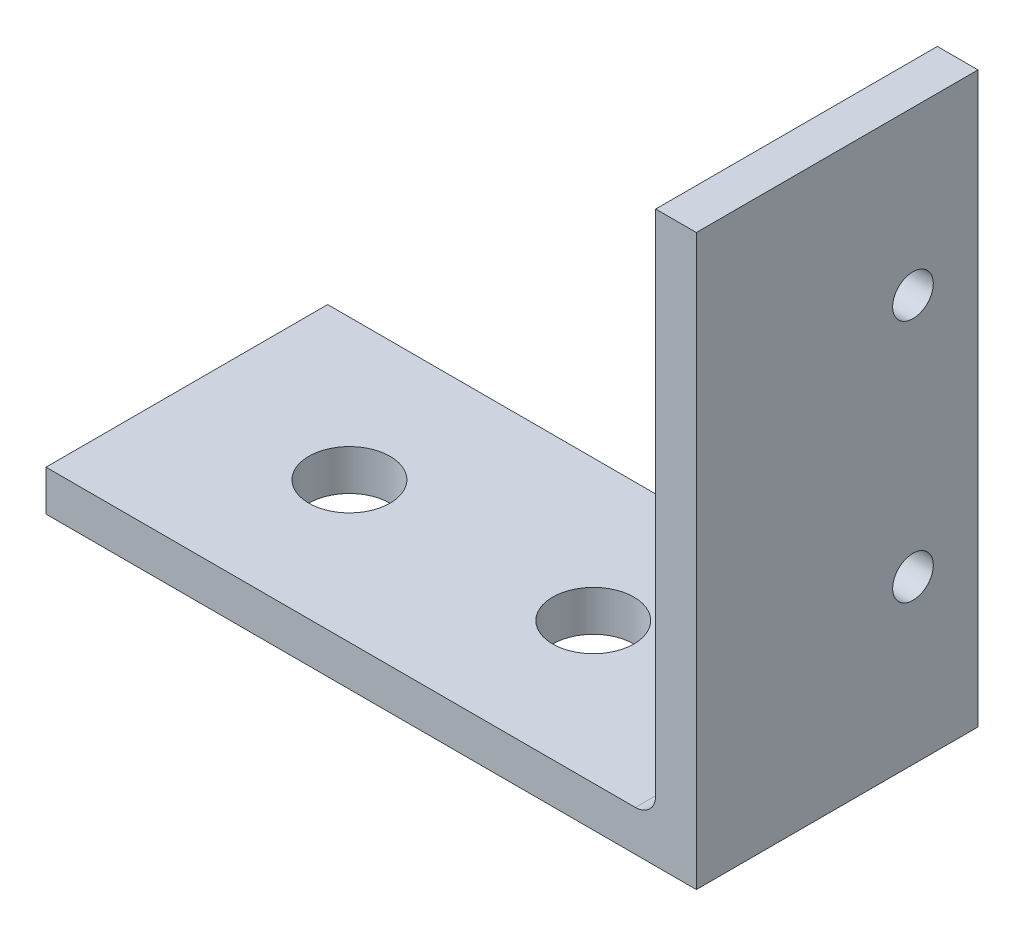
SolidWorks part; units mm, degrees
material "McMaster 6061-T6"
ref_plane "Front Plane" through (0, 0, 0) normal (0, 0, 1) x (1, 0, 0)
ref_plane "Top Plane" through (0, 0, 0) normal (0, 1, 0) x (1, 0, 0)
ref_plane "Right Plane" through (0, 0, 0) normal (1, 0, 0) x (0, 0, -1)
sketch "Sketch2" plane through (0, 0, 0) normal (0, 0, 1) x (1, 0, 0)
  line L0 (-25.4, 0) -> (25.4, 0)
  line L1 (25.4, 0) -> (25.4, 50.8)
  line L2 (25.4, 50.8) -> (22.225, 50.8)
  line L3 (22.225, 50.8) -> (22.225, 3.175)
  line L4 (22.225, 3.175) -> (-25.4, 3.175)
  line L5 (-25.4, 0) -> (-25.4, 3.175)
  line L6 (23.8125, 50.8) -> (25.4, 50.8) construction
  line L7 (-25.4, 1.5875) -> (-25.4, 0) construction
  dimension "Vert" = 50.8
  dimension "Horz" = 50.8
  dimension "Thickness" = 3.175
extrude "Boss-Extrude1" add sketch "Sketch2" along normal mid plane 22
fillet "Fillet1" radius 1.5875 1 edges at (22.225, 3.175, 0)
ref_plane "Contact Plane 1" through (0, 0, 0) normal (0, -1, 0) x (-1, 0, 0)
ref_plane "Contact Plane 2" through (25.4, 0, 0) normal (1, 0, 0) x (0, 0, -1)
ref_plane "Contact Plane 3" through (0, 3.175, 0) normal (0, 1, 0) x (1, 0, 0)
ref_plane "Contact Plane 4" through (22.225, 0, 0) normal (-1, 0, 0) x (0, 0, 1)
ref_plane "Contact Plane 5" through (0, 0, 11) normal (0, 0, 1) x (1, 0, 0)
ref_plane "Contact Plane 6" through (0, 0, -13.54) normal (0, 0, -1) x (-1, 0, 0)
sketch "Sketch3" plane through (0, 0, 11) normal (0, 0, 1) x (1, 0, 0)
  line L0 (-25.4, 0) -> (25.4, 0) construction
  line L1 (6.0591, 71.0024) -> (30.483, 71.0024)
  line L2 (6.0591, 71.0024) -> (6.0591, 44.45)
  line L3 (6.0591, 44.45) -> (30.483, 44.45)
  line L4 (30.483, 71.0024) -> (30.483, 44.45)
  dimension "D1" = 44.45
extrude "Cut-Extrude1" cut sketch "Sketch3" against normal through all
sketch "Sketch4" plane through (0, 0, 0) normal (0, -1, 0) x (1, 0, 0)
  line L0 (-25.4, 0) -> (-12.7, 0) construction
  line L3 (-25.4, 11) -> (-25.4, -11) construction
  line L4 (-12.7, 0) -> (6.35, 0) construction
  line L5 (6.35, 0) -> (25.4, 0) construction
  line L6 (25.4, 11) -> (25.4, -11) construction
  circle A0 centre (-12.7, 0) radius 3.175
  circle A1 centre (6.35, 0) radius 3.175
  dimension "D1" = 6.35
  dimension "D2" = 12.7
  dimension "D3" = 19.05
extrude "Cut-Extrude2" cut sketch "Sketch4" against normal through all
sketch "Sketch5" plane through (25.4, 0, 0) normal (1, 0, 0) x (0, 0, -1)
  line L0 (5.92, 0) -> (5.92, 12.7) construction
  line L1 (5.92, 12.7) -> (5.92, 31.75) construction
  line L2 (5.92, 31.75) -> (5.92, 44.45) construction
  line L5 (-11, 44.45) -> (11, 44.45) construction
  line L6 (-11, 0) -> (11, 0) construction
  line L7 (11, 44.45) -> (11, 4.7625) construction
  circle A0 centre (5.92, 31.75) radius 1.5875
  circle A1 centre (5.92, 12.7) radius 1.5875
  point P9 (0, 44.1007)
  point P10 (0, 0)
  point P12 (0, 5.5348)
  dimension "D2" = 3.175
  dimension "D1" = 12.7
  dimension "D3" = 5.08
extrude "Cut-Extrude3" cut sketch "Sketch5" against normal through all
equation "\"D1@Fillet1\"=\"Thickness@Sketch2\"/2"
